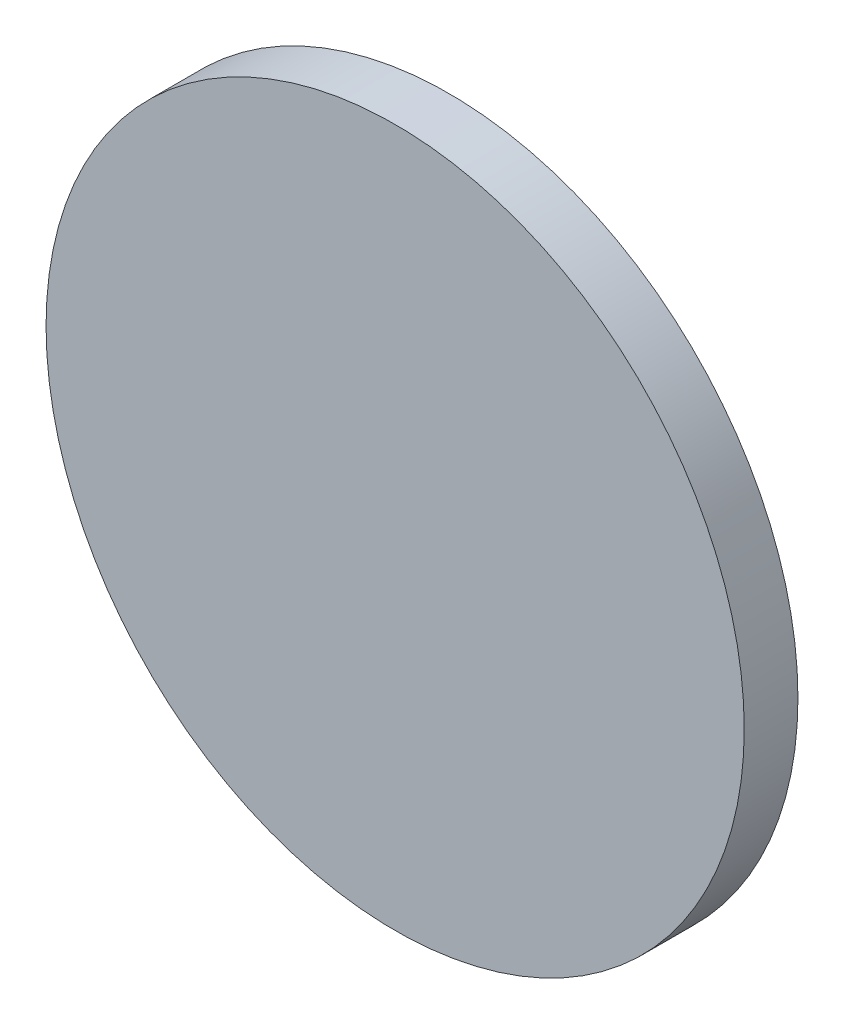
SolidWorks part; units mm, degrees
ref_plane "Front Plane" through (0, 0, 0) normal (0, 0, 1) x (1, 0, 0)
ref_plane "Top Plane" through (0, 0, 0) normal (0, 1, 0) x (1, 0, 0)
ref_plane "Right Plane" through (0, 0, 0) normal (1, 0, 0) x (0, 0, -1)
sketch "Sketch3" plane through (0, 0, 0) normal (0, 0, 1) x (1, 0, 0)
  line L0 (0, 0) -> (0, 330.2) construction
  circle A0 centre (0, 0) radius 330.2
  dimension "D1" = 660.4
extrude "Boss-Extrude2" add sketch "Sketch3" along normal blind 50.8
sketch "Sketch4" plane through (0, 0, 50.8) normal (0, 0, 1) x (1, 0, 0)
  line L0 (0, 0) -> (11.2248, 330.0092) construction
  circle A0 centre (0, 0) radius 330.2 construction
sketch "Sketch5" plane through (0, 0, 0) normal (0, 0, -1) x (-1, 0, 0)
  line L0 (0, 0) -> (-11.2248, 330.0092) construction
